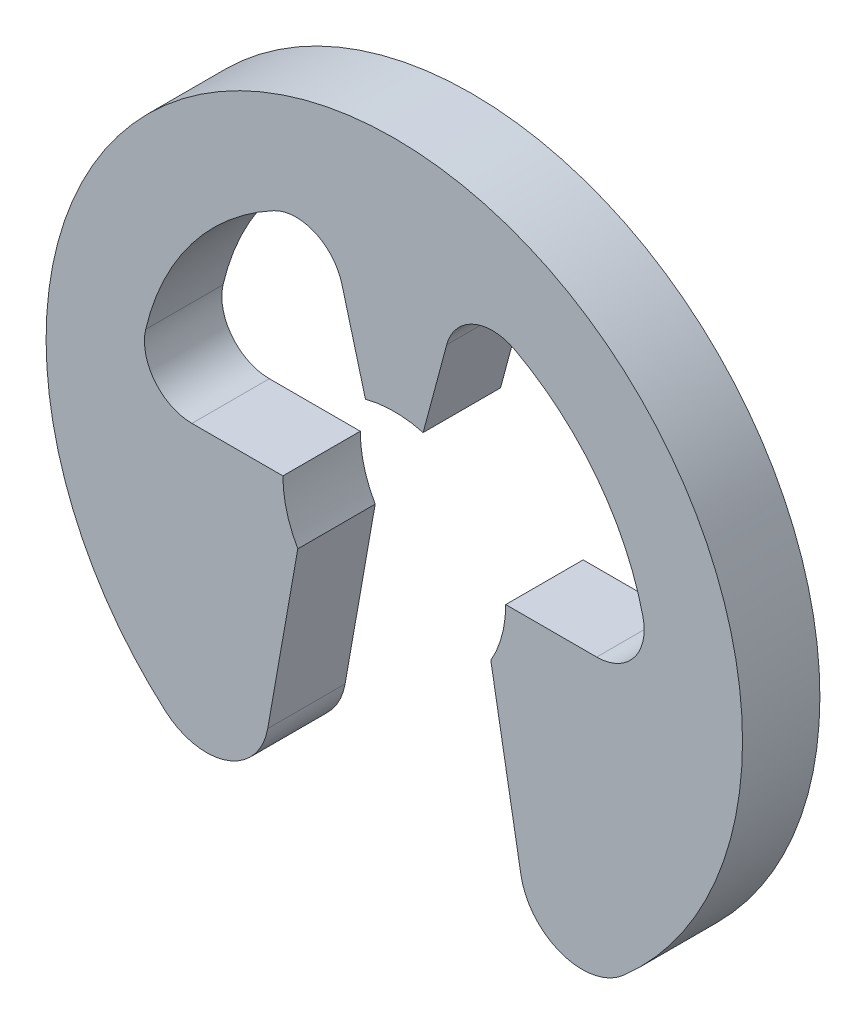
SolidWorks part; units mm, degrees
ref_plane "Plane1" through (0, 0, 0) normal (0, 0, 1) x (1, 0, 0)
ref_plane "Plane2" through (0, 0, 0) normal (0, 1, 0) x (1, 0, 0)
ref_plane "Plane3" through (0, 0, 0) normal (1, 0, 0) x (0, 0, -1)
sketch "Clipboard" plane through (0, 0, 0) normal (0, 0, 1) x (1, 0, 0)
  line L0 (0, 0) -> (0.3, 0)
  circle A0 centre (0, 0) radius 0.32
  circle A1 centre (0, 0) radius 1
sketch "BodySke" plane through (0, 0, 0) normal (0, 0, 1) x (1, 0, 0)
  line L0 (-0.7581, 0) -> (0.7581, 0) construction
  line L1 (0, 0) -> (0, 0.36) construction
  line L2 (0, 0) -> (0.1962, 0.7323) construction
  line L3 (0, 0) -> (0.3118, -0.18) construction
  line L4 (0, 0) -> (-0.1962, 0.7323) construction
  line L5 (0, 0) -> (-0.3118, -0.18) construction
  line L6 (0.3118, -0.18) -> (0.409, -0.7316)
  line L7 (-0.3118, -0.18) -> (-0.409, -0.7316)
  line L9 (0.36, 0) -> (0.6538, 0)
  line L10 (-0.36, 0) -> (-0.6538, 0)
  line L11 (0.0932, 0.3477) -> (0.1692, 0.6315)
  line L12 (-0.0932, 0.3477) -> (-0.1692, 0.6315)
  circle A0 centre (0, 0) radius 0.36 construction
  arc A1 (0.8032, 0.1885) -> (0.39, 0.727) centre (0, 0) ccw
  arc A2 (0.739, -0.8482) -> (-0.739, -0.8482) centre (0, 0) ccw
  arc A3 (0.3118, -0.18) -> (0.36, 0) centre (0, 0) ccw
  arc A4 (-0.39, 0.727) -> (-0.8032, 0.1885) centre (0, 0) ccw
  arc A5 (-0.36, 0) -> (-0.3118, -0.18) centre (0, 0) ccw
  arc A6 (-0.0932, 0.3477) -> (0.0932, 0.3477) centre (0, 0) cw
  arc A7 (0.39, 0.727) -> (0.1692, 0.6315) centre (0.3174, 0.5918) ccw
  arc A8 (0.409, -0.7316) -> (0.739, -0.8482) centre (0.607, -0.6967) ccw
  arc A9 (-0.739, -0.8482) -> (-0.409, -0.7316) centre (-0.607, -0.6967) ccw
  arc A10 (-0.8032, 0.1885) -> (-0.6538, 0) centre (-0.6538, 0.1535) ccw
  arc A11 (-0.1692, 0.6315) -> (-0.39, 0.727) centre (-0.3174, 0.5918) ccw
  arc A12 (0.6538, 0) -> (0.8032, 0.1885) centre (0.6538, 0.1535) ccw
  dimension "OutsideDia" = 11.4543
  dimension "TipRad" = 0.7705
  dimension "CavityDia" = 9.1543
  dimension "CavityFilletRad" = 0.7102
  dimension "D1" = 30
  dimension "D3" = 30
  dimension "D4" = 20
extrude "Body" add sketch "BodySke" against normal blind 0.25
equation "' \"FreeID@Clipboard\" = 0.64"
equation "' \"Thickness@Body\" = 0.25"
equation "' \"GrooveDia@BodySke\" = 0.72"
equation "' \"FreeOD@Clipboard\" = 2"
equation "' \"Bridge@Clipboard\" = 0.3"
equation "' \"FreeID@Clipboard\" = 19.5"
equation "' \"Thickness@Body\" = 1.3"
equation "' \"GrooveDia@BodySke\" = 20.00"
equation "' \"FreeOD@Clipboard\" = 37.1"
equation "' \"Bridge@Clipboard\" = 3.3"
equation "\"OutsideDia@BodySke\" = ( \"GrooveDia@BodySke\"  /  \"FreeID@Clipboard\" )  * \"FreeOD@Clipboard\""
equation "\"CavityDia@BodySke\" = \"OutsideDia@BodySke\"  - 2 * \"Bridge@Clipboard\""
equation "\"CavityFilletRad@BodySke\" =  (\"CavityDia@BodySke\" - \"GrooveDia@BodySke\") / 2 * 0.33"
equation "\"TipRad@BodySke\" = 0.67 * \"Bridge@Clipboard\""
